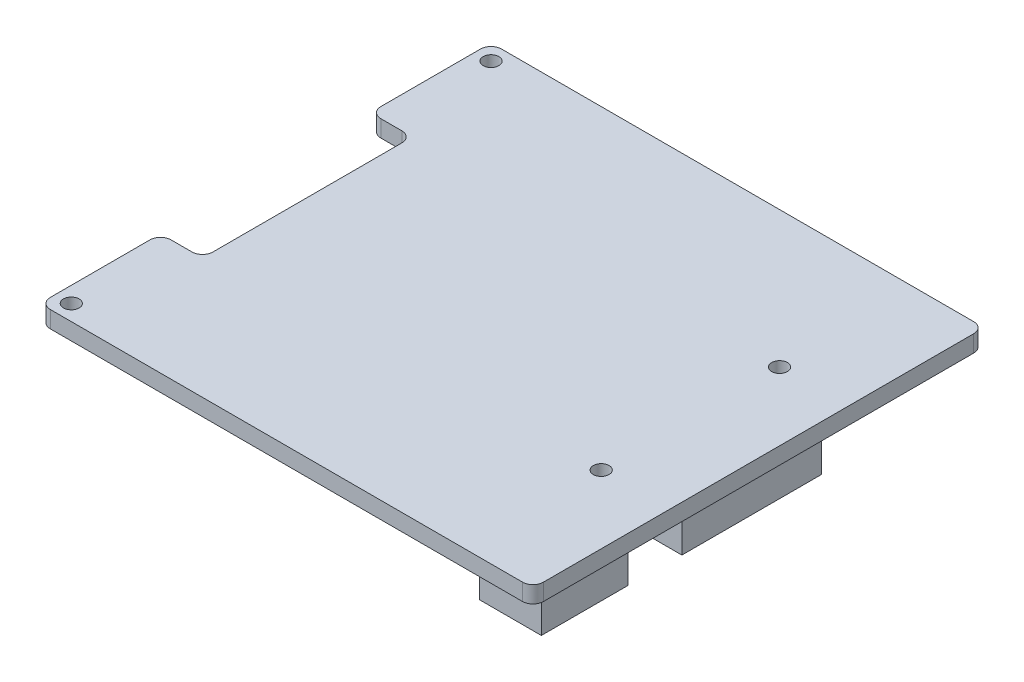
SolidWorks part; units mm, degrees
ref_plane "Front" through (0, 0, 0) normal (0, 0, 1) x (1, 0, 0)
ref_plane "Top" through (0, 0, 0) normal (0, 1, 0) x (1, 0, 0)
ref_plane "Right" through (0, 0, 0) normal (1, 0, 0) x (0, 0, -1)
sketch "草图1" plane through (0, 0, 0) normal (0, 1, 0) x (1, 0, 0)
  line L1 (23.5, -21.5) -> (-23.5, -21.5)
  line L2 (23.5, -21.5) -> (23.5, 21.5)
  line L3 (23.5, 21.5) -> (-23.5, 21.5)
  line L4 (-23.5, -21.5) -> (-23.5, 21.5)
  line L5 (23.5, -21.5) -> (-23.5, 21.5) construction
  line L6 (23.5, 21.5) -> (-23.5, -21.5) construction
  point P0 (0, 0)
  dimension "D1" = 47
  dimension "D2" = 43
extrude "凸台-拉伸1" add sketch "草图1" along normal blind 1.6
sketch "草图2" plane through (0, 1.6, 0) normal (0, 1, 0) x (1, 0, 0)
  line L0 (0, 42.4549) -> (0, -30.2173) construction
  line L1 (-42.0205, 0) -> (45.9295, 0) construction
  line L2 (-23.5, 21.5) -> (-23.5, -21.5) construction
  circle A0 centre (-22, 20) radius 0.75
  circle A2 centre (-22, -20) radius 0.75
  dimension "D1" = 1.5
  dimension "D2" = 40
  dimension "D3" = 1.5
extrude "切除-拉伸1" cut sketch "草图2" against normal through all
sketch "草图3" plane through (0, 1.6, 0) normal (0, 1, 0) x (1, 0, 0)
  line L0 (-33.0397, 0) -> (39.9423, 0) construction
  line L1 (23.5, -21.5) -> (23.5, 21.5) construction
  circle A0 centre (17, 8.5) radius 0.75
  circle A1 centre (17, -8.5) radius 0.75
  dimension "D1" = 1.5
  dimension "D2" = 17
  dimension "D3" = 6.5
extrude "切除-拉伸2" cut sketch "草图3" against normal through all
fillet "圆角1" radius 1 4 edges at (-23.5, 0.8, -21.5) (23.5, 0.8, -21.5) (23.5, 0.8, 21.5) (-23.5, 0.8, 21.5)
sketch "草图4" plane through (0, 0, 0) normal (0, -1, 0) x (1, 0, 0)
  line L0 (-26.4528, 0) -> (22.6479, 0) construction
  line L1 (22.6479, 0) -> (26.6944, 0) construction
  line L2 (-23.5, -20.5) -> (-23.5, 20.5) construction
  line L3 (-19.5, -10) -> (-23.5, -10)
  line L4 (-19.5, -10) -> (-19.5, 10)
  line L5 (-19.5, 10) -> (-23.5, 10)
  line L6 (-23.5, -10) -> (-23.5, 10)
  line L7 (-19.5, -10) -> (-23.5, 10) construction
  line L8 (-19.5, 10) -> (-23.5, -10) construction
  point P4 (-21.5, 0)
  dimension "D1" = 20
  dimension "D2" = 4
extrude "切除-拉伸3" cut sketch "草图4" against normal through all
fillet "圆角2" radius 1 2 edges at (-23.5, 0.8, -10) (-23.5, 0.8, 10)
fillet "圆角3" radius 1 2 edges at (-19.5, 0.8, 10) (-19.5, 0.8, -10)
sketch "草图5" plane through (0, 0, 0) normal (0, 1, 0) x (1, 0, 0)
  line L0 (-28.3986, 0) -> (27.9233, 0) construction
  line L2 (-12.0011, 17.1105) -> (-17.0709, 17.1105)
  line L3 (-12.0011, 17.1105) -> (-12.0011, -17.1105)
  line L4 (-12.0011, -17.1105) -> (-17.0709, -17.1105)
  line L5 (-17.0709, 17.1105) -> (-17.0709, -17.1105)
  line L6 (-12.0011, 17.1105) -> (-17.0709, -17.1105) construction
  line L7 (-12.0011, -17.1105) -> (-17.0709, 17.1105) construction
  line L8 (23.2654, 6.2508) -> (17.3282, 6.2508)
  line L9 (23.2654, 6.2508) -> (23.2654, -7.0754)
  line L10 (23.2654, -7.0754) -> (17.3282, -7.0754)
  line L11 (17.3282, 6.2508) -> (17.3282, -7.0754)
  line L12 (23.2654, 6.2508) -> (17.3282, -7.0754) construction
  line L13 (23.2654, -7.0754) -> (17.3282, 6.2508) construction
  line L14 (23.205, -12.1685) -> (17.3282, -12.1685)
  line L15 (23.205, -12.1685) -> (23.205, -20.4069)
  line L16 (23.205, -20.4069) -> (17.3282, -20.4069)
  line L17 (17.3282, -12.1685) -> (17.3282, -20.4069)
  line L18 (23.205, -12.1685) -> (17.3282, -20.4069) construction
  line L19 (23.205, -20.4069) -> (17.3282, -12.1685) construction
  point P2 (-14.536, 0)
  point P8 (20.2968, -0.4123)
  point P13 (20.2666, -16.2877)
extrude "凸台-拉伸2" add sketch "草图5" against normal blind 3
